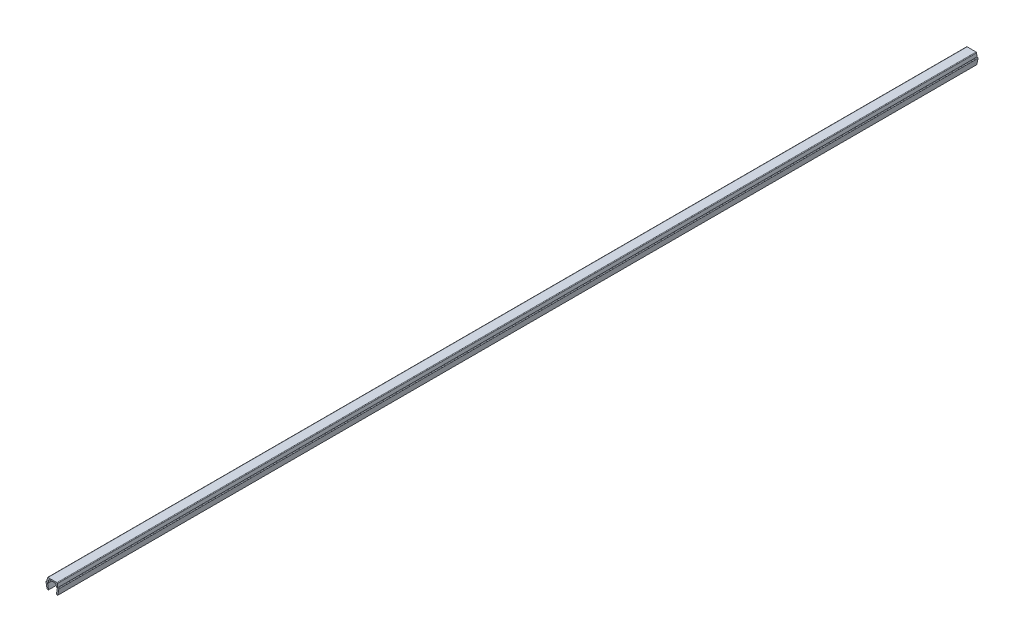
SolidWorks part; units mm, degrees
ref_plane "Front Plane" through (0, 0, 0) normal (0, 0, 1) x (1, 0, 0)
ref_plane "Top Plane" through (0, 0, 0) normal (0, 1, 0) x (1, 0, 0)
ref_plane "Right Plane" through (0, 0, 0) normal (1, 0, 0) x (0, 0, -1)
ref_plane "Plane1" through (0, 0, 0) normal (0, 0, 1) x (1, 0, 0)
sketch "Sketch1" plane through (0, 0, 0) normal (0, 0, 1) x (1, 0, 0)
  line L0 (-3.6, 3.35) -> (-3, 0)
  line L1 (-3, 0) -> (-2.2, 0)
  line L2 (-2.2, 0) -> (-2.7352, 2.9883)
  line L3 (-2.3907, 3.4) -> (-2.2, 3.4)
  line L4 (-2.2, 3.4) -> (-2.0705, 4.8805)
  line L5 (-1.7218, 5.2) -> (1.7218, 5.2)
  line L6 (2.0705, 4.8805) -> (2.2, 3.4)
  line L7 (2.2, 3.4) -> (2.3907, 3.4)
  line L8 (2.7352, 2.9883) -> (2.2, 0)
  line L9 (2.2, 0) -> (3, 0)
  line L10 (3, 0) -> (3.6, 3.35)
  line L11 (3.25, 3.7) -> (3, 3.7)
  line L12 (3, 3.7) -> (2.8355, 5.5805)
  line L13 (2.4868, 5.9) -> (-2.4868, 5.9)
  line L14 (-2.8355, 5.5805) -> (-3, 3.7)
  line L15 (-3, 3.7) -> (-3.25, 3.7)
  arc A0 (-2.7352, 2.9883) -> (-2.3907, 3.4) centre (-2.3907, 3.05) cw
  arc A1 (-2.0705, 4.8805) -> (-1.7218, 5.2) centre (-1.7218, 4.85) cw
  arc A2 (1.7218, 5.2) -> (2.0705, 4.8805) centre (1.7218, 4.85) cw
  arc A3 (2.3907, 3.4) -> (2.7352, 2.9883) centre (2.3907, 3.05) cw
  arc A4 (3.6, 3.35) -> (3.25, 3.7) centre (3.25, 3.35) ccw
  arc A5 (2.8355, 5.5805) -> (2.4868, 5.9) centre (2.4868, 5.55) ccw
  arc A6 (-2.4868, 5.9) -> (-2.8355, 5.5805) centre (-2.4868, 5.55) ccw
  arc A7 (-3.25, 3.7) -> (-3.6, 3.35) centre (-3.25, 3.35) ccw
extrude "Boss-Extrude1" add sketch "Sketch1" against normal mid plane 515
